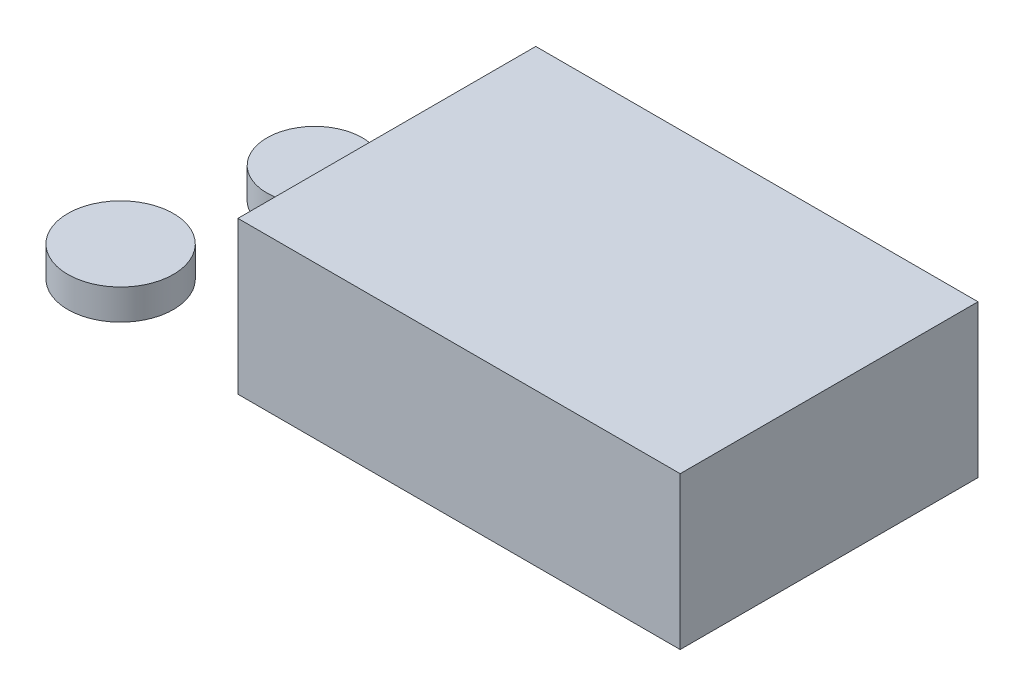
SolidWorks part; units mm, degrees
ref_plane "前视基准面" through (0, 0, 0) normal (0, 0, 1) x (1, 0, 0)
ref_plane "上视基准面" through (0, 0, 0) normal (0, 1, 0) x (1, 0, 0)
ref_plane "右视基准面" through (0, 0, 0) normal (1, 0, 0) x (0, 0, -1)
other "Configuration Table"
sketch "草图1" plane through (0, 0, 0) normal (0, 1, 0) x (1, 0, 0)
  line L1 (-72.5813, -48.8785) -> (72.5813, -48.8785)
  line L2 (-72.5813, -48.8785) -> (-72.5813, 48.8785)
  line L3 (-72.5813, 48.8785) -> (72.5813, 48.8785)
  line L4 (72.5813, -48.8785) -> (72.5813, 48.8785)
  line L5 (0, 48.8785) -> (0, -48.8785) construction
  line L6 (-72.5813, 0) -> (72.5813, 0) construction
  point P0 (0, 0)
extrude "凸台-拉伸1" add sketch "草图1" along normal blind 50
sketch "草图2" plane through (0, 0, 0) normal (0, 1, 0) x (1, 0, 0)
  circle A0 centre (-115.0307, 18.7853) radius 15.6982
extrude "凸台-拉伸2" add sketch "草图2" along normal blind 10 separate body
sketch "草图3" plane through (0, 0, 0) normal (0, 1, 0) x (1, 0, 0)
  circle A0 centre (-124.5696, -35.4049) radius 17.3343
extrude "凸台-拉伸3" add sketch "草图3" along normal blind 10 separate body
